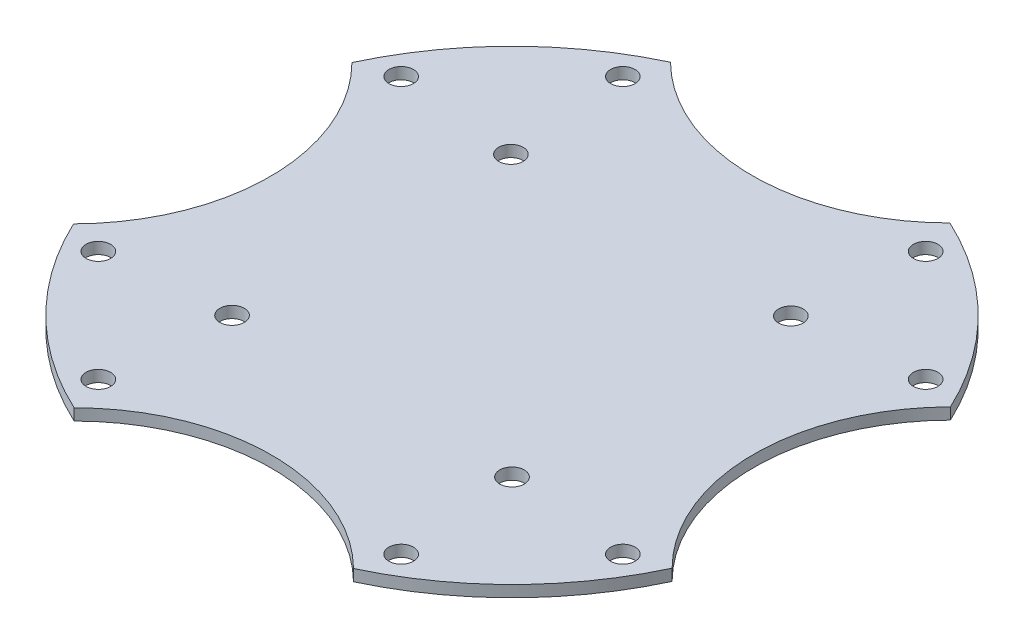
SolidWorks part; units mm, degrees
material "Thornel Mat VMA"
ref_plane "Front Plane" through (0, 0, 0) normal (0, 0, 1) x (1, 0, 0)
ref_plane "Top Plane" through (0, 0, 0) normal (0, 1, 0) x (1, 0, 0)
ref_plane "Right Plane" through (0, 0, 0) normal (1, 0, 0) x (0, 0, -1)
sketch "Sketch2" plane through (0, 0, 0) normal (0, 1, 0) x (1, 0, 0)
  line L0 (51.8715, 0) -> (39.5, 0) construction
  line L1 (31.4505, 0) -> (-50.2816, 0) construction
  line L2 (0, 0) -> (47.988, 27.7059) construction
  line L3 (0, 0) -> (27.499, 47.6297) construction
  line L4 (0, 0) -> (47.6297, -27.499) construction
  line L5 (0, 0) -> (27.7059, -47.988) construction
  line L6 (0, 0) -> (-27.499, -47.6297) construction
  line L7 (0, 0) -> (-47.988, -27.7059) construction
  line L8 (0, 0) -> (-47.6297, 27.499) construction
  line L9 (0, 0) -> (-27.7059, 47.988) construction
  line L10 (-18.2579, 47.988) -> (-18.2579, -49.3349) construction
  line L11 (18.2579, -49.3349) -> (18.2579, 47.9749) construction
  line L12 (-25.2062, 18.1164) -> (29.4239, 18.1164) construction
  line L13 (-22.8588, -18.2579) -> (26.0095, -18.2579) construction
  arc A0 (-18.2579, 38.9313) -> (-38.9974, 18.1164) centre (0, 0) ccw
  arc A1 (-15.3073, 36.4134) -> (-36.4688, 15.175) centre (0, 0) ccw construction
  circle A2 centre (19.75, 34.208) radius 1.6
  circle A3 centre (34.208, 19.75) radius 1.6
  circle A4 centre (19.75, -34.208) radius 1.6
  circle A5 centre (34.208, -19.75) radius 1.6
  circle A6 centre (-34.208, -19.75) radius 1.6
  circle A7 centre (-19.75, -34.208) radius 1.6
  circle A8 centre (-19.75, 34.208) radius 1.6
  circle A9 centre (-34.208, 19.75) radius 1.6
  arc A10 (18.1164, 38.9974) -> (-18.2579, 38.9313) centre (-0.1039, 57.2177) cw
  arc A11 (38.9974, -18.1164) -> (38.9313, 18.2579) centre (57.2177, 0.1039) cw
  arc A12 (-18.1164, -38.9974) -> (18.2579, -38.9313) centre (0.1039, -57.2177) cw
  arc A13 (-38.9974, 18.1164) -> (-38.9313, -18.2579) centre (-57.2177, -0.1039) cw
  arc A14 (-36.4134, -15.3073) -> (-15.175, -36.4688) centre (0, 0) ccw construction
  arc A15 (-38.9313, -18.2579) -> (-18.1164, -38.9974) centre (0, 0) ccw
  arc A16 (38.9313, 18.2579) -> (18.1164, 38.9974) centre (0, 0) ccw
  arc A17 (36.4134, 15.3073) -> (15.175, 36.4688) centre (0, 0) ccw construction
  arc A18 (18.2579, -38.9313) -> (38.9974, -18.1164) centre (0, 0) ccw
  arc A19 (15.3073, -36.4134) -> (36.4688, -15.175) centre (0, 0) ccw construction
  circle A20 centre (-18.2579, 18.1164) radius 1.6
  circle A21 centre (18.2579, 18.1164) radius 1.6
  circle A22 centre (-18.2579, -18.2579) radius 1.6
  circle A23 centre (18.2579, -18.2579) radius 1.6
  point P19 (0, 0)
  point P36 (0, 0)
  point P47 (0, 0)
  dimension "D1" = 86
  dimension "D2" = 79
  dimension "D6" = 3.2
  dimension "D7" = 3.2
  dimension "D10" = 3.2
  dimension "D11" = 3.2
  dimension "D12" = 3.2
  dimension "D13" = 3.2
  dimension "D3" = 30
  dimension "D4" = 30
  dimension "D9" = 4
  dimension "D5" = 4
  dimension "D8" = 4
extrude "Boss-Extrude1" add sketch "Sketch2" along normal blind 1.5
